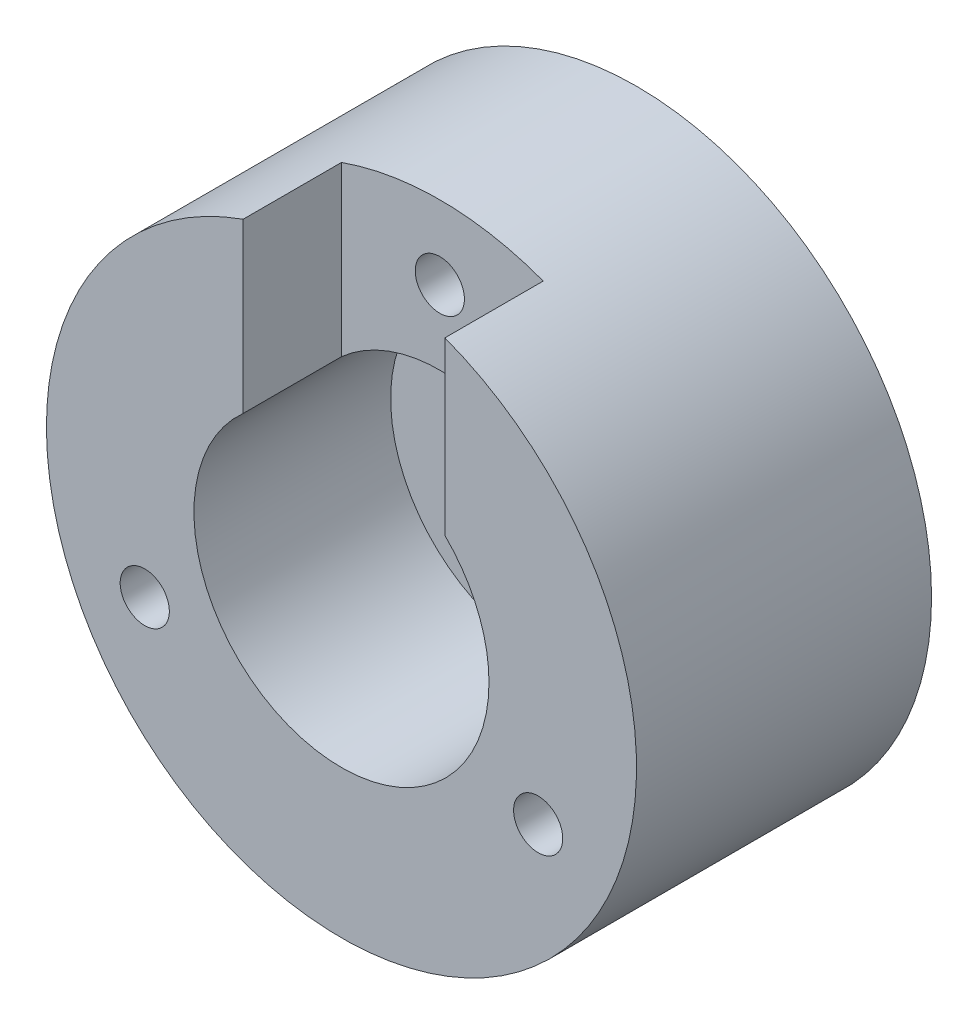
SolidWorks part; units mm, degrees
ref_plane "Front Plane" through (0, 0, 0) normal (0, 0, 1) x (1, 0, 0)
ref_plane "Top Plane" through (0, 0, 0) normal (0, 1, 0) x (1, 0, 0)
ref_plane "Right Plane" through (0, 0, 0) normal (1, 0, 0) x (0, 0, -1)
sketch "Sketch1" plane through (0, 0, 0) normal (0, 0, 1) x (1, 0, 0)
  circle A0 centre (0, 0) radius 60
  dimension "D1" = 120
extrude "Boss-Extrude1" add sketch "Sketch1" along normal blind 60
sketch "Sketch2" plane through (0, 0, 60) normal (0, 0, 1) x (1, 0, 0)
  circle A0 centre (0, 0) radius 30
  dimension "D1" = 60
extrude "Cut-Extrude1" cut sketch "Sketch2" against normal blind 40
sketch "Sketch3" plane through (0, 0, 20) normal (0, 0, 1) x (1, 0, 0)
  circle A0 centre (0, 0) radius 10
  dimension "D1" = 20
extrude "Cut-Extrude2" cut sketch "Sketch3" against normal blind 40
sketch "Sketch4" plane through (0, 0, 60) normal (0, 0, 1) x (1, 0, 0)
  circle A0 centre (0, 45) radius 5
  dimension "D1" = 10
  dimension "D2" = 0
  dimension "D3" = 45
extrude "Cut-Extrude3" cut sketch "Sketch4" against normal blind 100
sketch "Sketch5" plane through (0, 0, 60) normal (0, 0, 1) x (1, 0, 0)
  circle A0 centre (-40, -20) radius 5
  circle A1 centre (40, -20) radius 5
  dimension "D1" = 10
  dimension "D2" = 10
  dimension "D3" = 20
  dimension "D4" = 20
  dimension "D5" = 40
  dimension "D6" = 40
extrude "Cut-Extrude4" cut sketch "Sketch5" against normal blind 100
sketch "Sketch6" plane through (0, 0, 60) normal (0, 0, 1) x (1, 0, 0)
  line L0 (-20, 56.5685) -> (-20, 22.3607)
  line L1 (21.0287, 56.1942) -> (21.0287, 21.3961)
  arc A0 (21.0287, 21.3961) -> (-20, 22.3607) centre (0, 0) ccw
  circle A1 centre (0, 0) radius 30 construction
  arc A2 (21.0287, 56.1942) -> (-20, 56.5685) centre (0, 0) ccw
  circle A3 centre (0, 0) radius 60 construction
  dimension "D1" = 20
  dimension "D2" = 21.0287
extrude "Cut-Extrude5" cut sketch "Sketch6" against normal blind 20
